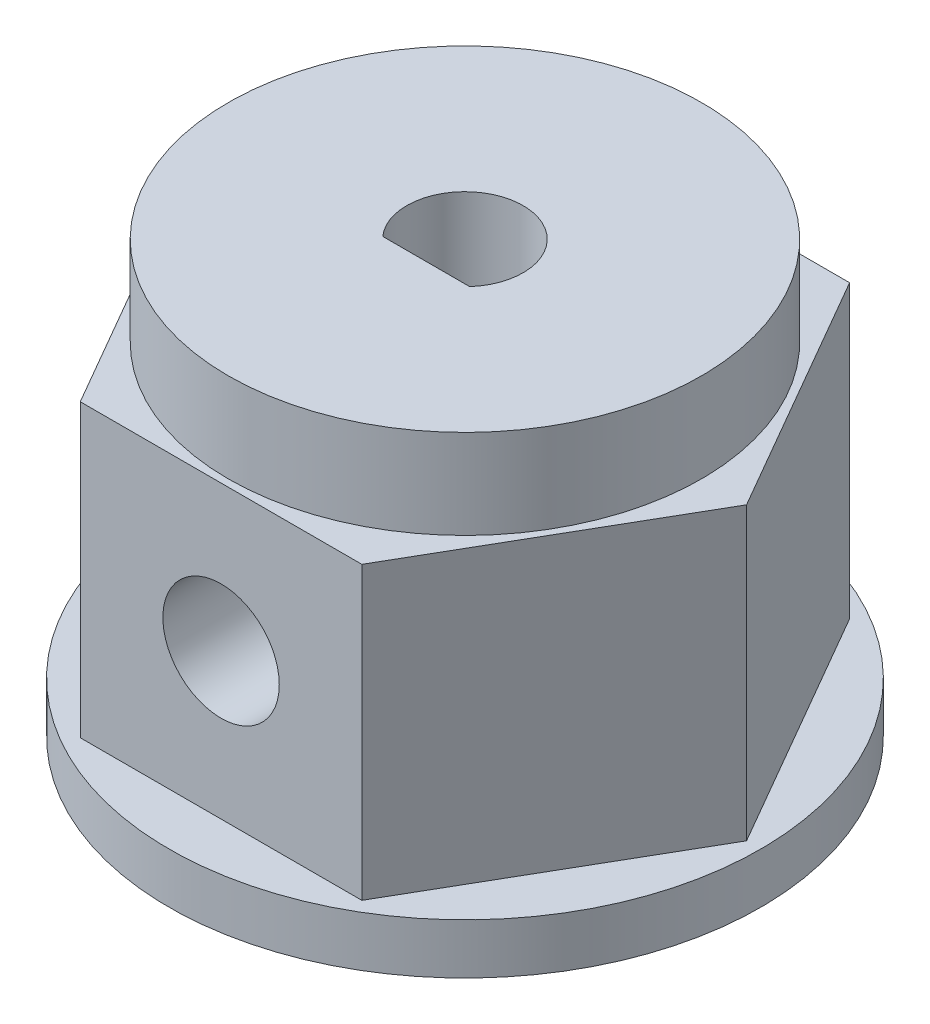
SolidWorks part; units mm, degrees
ref_plane "Front Plane" through (0, 0, 0) normal (0, 0, 1) x (1, 0, 0)
ref_plane "Top Plane" through (0, 0, 0) normal (0, 1, 0) x (1, 0, 0)
ref_plane "Right Plane" through (0, 0, 0) normal (1, 0, 0) x (0, 0, -1)
sketch "Sketch1" plane through (0, 0, 0) normal (0, 1, 0) x (1, 0, 0)
  line L1 (7.2573, 0) -> (3.6286, 6.285)
  line L2 (3.6286, 6.285) -> (-3.6286, 6.285)
  line L3 (-3.6286, 6.285) -> (-7.2573, 0)
  line L4 (-7.2573, 0) -> (-3.6286, -6.285)
  line L5 (-3.6286, -6.285) -> (3.6286, -6.285)
  line L6 (3.6286, -6.285) -> (7.2573, 0)
  circle A0 centre (0, 0) radius 6.285 construction
  dimension "D1" = 12.57
extrude "Boss-Extrude1" add sketch "Sketch1" along normal blind 7.5
sketch "Sketch2" plane through (0, 7.5, 0) normal (0, 1, 0) x (1, 0, 0)
  circle A0 centre (0, 0) radius 6.1
  dimension "D1" = 12.2
extrude "Boss-Extrude2" add sketch "Sketch2" along normal blind 2.3
sketch "Sketch3" plane through (0, 0, 0) normal (0, -1, 0) x (1, 0, 0)
  circle A0 centre (0, 0) radius 7.625
  dimension "D1" = 15.25
extrude "Boss-Extrude3" add sketch "Sketch3" along normal blind 1.3
sketch "Sketch4" plane through (0, 9.8, 0) normal (0, 1, 0) x (1, 0, 0)
  line L0 (-1.12, -0.9978) -> (1.12, -0.9978)
  arc A0 (1.12, -0.9978) -> (-1.12, -0.9978) centre (0, 0) ccw
  dimension "D1" = 3
  dimension "D2" = 2.24
extrude "Cut-Extrude1" cut sketch "Sketch4" against normal through all
sketch "Sketch5" plane through (0, 0, 6.285) normal (0, 0, 1) x (1, 0, 0)
  circle A0 centre (0, 3.75) radius 1.5
  dimension "D1" = 3
  dimension "D2" = 3.75
extrude "Cut-Extrude2" cut sketch "Sketch5" against normal up to next
